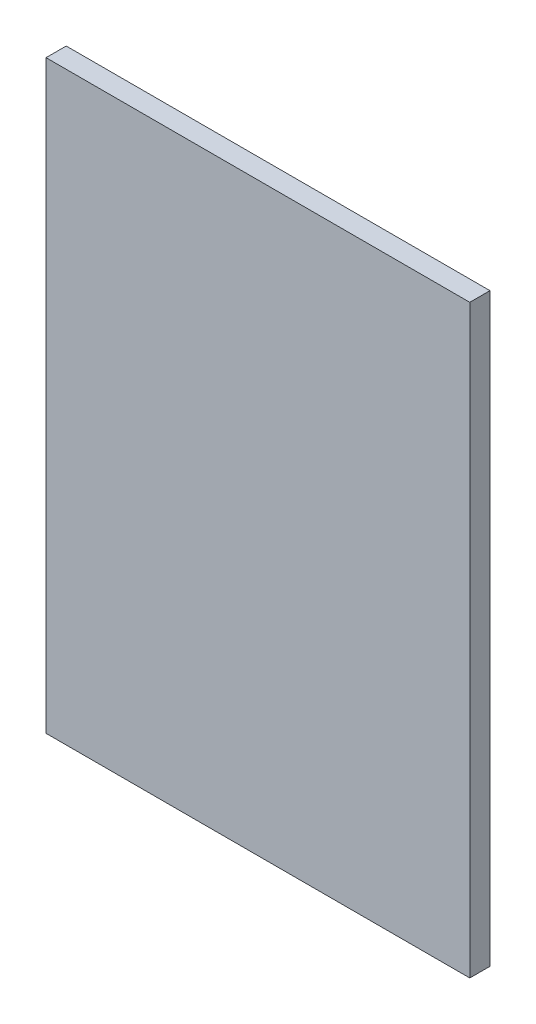
SolidWorks part; units mm, degrees
ref_plane "Front Plane" through (0, 0, 0) normal (0, 0, 1) x (1, 0, 0)
ref_plane "Top Plane" through (0, 0, 0) normal (0, 1, 0) x (1, 0, 0)
ref_plane "Right Plane" through (0, 0, 0) normal (1, 0, 0) x (0, 0, -1)
sketch "Sketch1" plane through (0, 0, 0) normal (0, 0, 1) x (1, 0, 0)
  line L1 (-23.449, 14.6777) -> (18.551, 14.6777)
  line L2 (-23.449, 14.6777) -> (-23.449, -43.3223)
  line L3 (-23.449, -43.3223) -> (18.551, -43.3223)
  line L4 (18.551, 14.6777) -> (18.551, -43.3223)
  dimension "D1" = 42
  dimension "D2" = 58
extrude "Boss-Extrude1" add sketch "Sketch1" against normal blind 2
